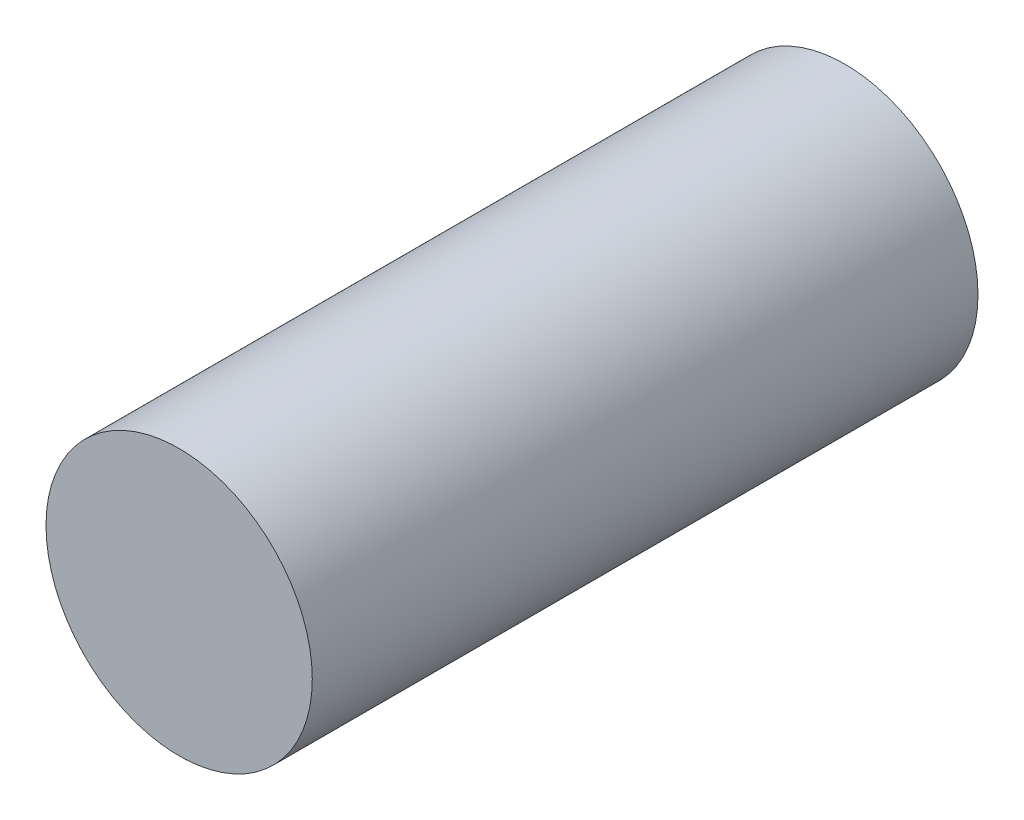
SolidWorks part; units mm, degrees
ref_plane "Front Plane" through (0, 0, 0) normal (0, 0, 1) x (1, 0, 0)
ref_plane "Top Plane" through (0, 0, 0) normal (0, 1, 0) x (1, 0, 0)
ref_plane "Right Plane" through (0, 0, 0) normal (1, 0, 0) x (0, 0, -1)
sketch "Sketch1" plane through (0, 0, 0) normal (0, 0, 1) x (1, 0, 0)
  circle A0 centre (-4.5267, -2.1859) radius 4
extrude "Boss-Extrude2" add sketch "Sketch1" along normal blind 20 contours A0
sketch "Sketch3" plane through (0, 0, 0) normal (0, 0, -1) x (-1, 0, 0)
  circle A0 centre (4.8801, -2.0407) radius 1.5
extrude "Cut-Extrude2" cut sketch "Sketch3" against normal blind 3
